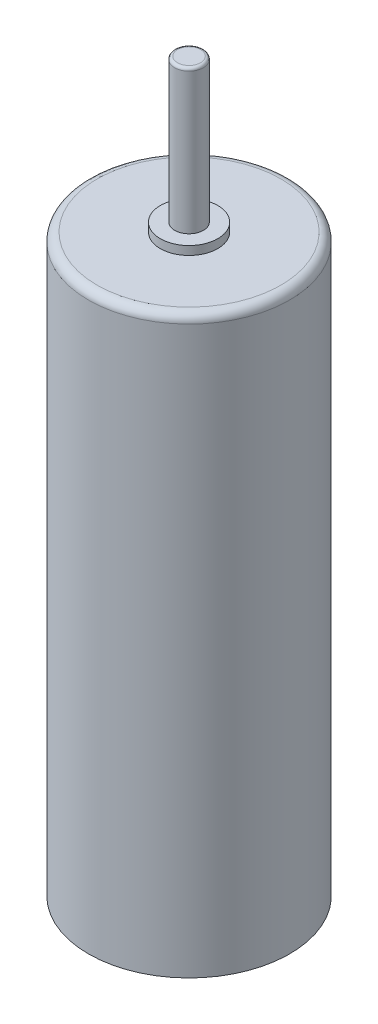
SolidWorks part; units mm, degrees
ref_plane "Front Plane" through (0, 0, 0) normal (0, 0, 1) x (1, 0, 0)
ref_plane "Top Plane" through (0, 0, 0) normal (0, 1, 0) x (1, 0, 0)
ref_plane "Right Plane" through (0, 0, 0) normal (1, 0, 0) x (0, 0, -1)
sketch "Sketch1" plane through (0, 0, 0) normal (0, 1, 0) x (1, 0, 0)
  circle A0 centre (0, 0) radius 3.5
  dimension "D1" = 7
extrude "Boss-Extrude1" add sketch "Sketch1" along normal blind 20
fillet "Fillet1" radius 0.3 1 edges at (0, 20, 3.5)
sketch "Sketch2" plane through (0, 20, 0) normal (0, 1, 0) x (1, 0, 0)
  circle A0 centre (0, 0) radius 1
  dimension "D1" = 2
extrude "Boss-Extrude2" add sketch "Sketch2" along normal blind 0.3
sketch "Sketch3" plane through (0, 20.3, 0) normal (0, 1, 0) x (1, 0, 0)
  circle A0 centre (0, 0) radius 0.5
  dimension "D1" = 1
extrude "Boss-Extrude3" add sketch "Sketch3" along normal blind 5
fillet "Fillet2" radius 0.1 1 edges at (0, 25.3, 0.5)
